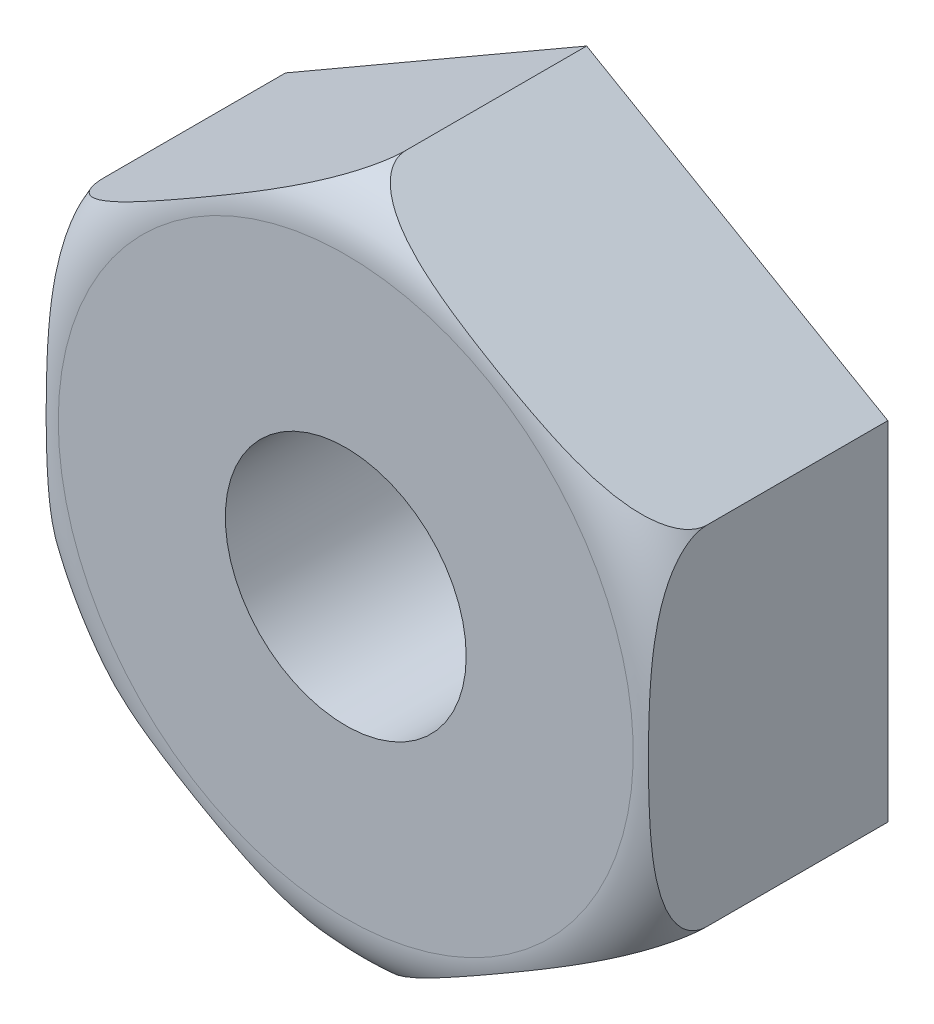
SolidWorks part; units mm, degrees
ref_plane "Front Plane" through (0, 0, 0) normal (0, 0, 1) x (1, 0, 0)
ref_plane "Top Plane" through (0, 0, 0) normal (0, 1, 0) x (1, 0, 0)
ref_plane "Right Plane" through (0, 0, 0) normal (1, 0, 0) x (0, 0, -1)
sketch "Sketch1" plane through (0, 0, 0) normal (0, 0, 1) x (1, 0, 0)
  line L1 (0, -5.7735) -> (5, -2.8868)
  line L2 (5, -2.8868) -> (5, 2.8868)
  line L3 (5, 2.8868) -> (0, 5.7735)
  line L4 (0, 5.7735) -> (-5, 2.8868)
  line L5 (-5, 2.8868) -> (-5, -2.8868)
  line L6 (-5, -2.8868) -> (0, -5.7735)
  circle A0 centre (0, 0) radius 5 construction
  dimension "D1" = 10
extrude "Boss-Extrude1" add sketch "Sketch1" along normal mid plane 4
sketch "Sketch3" plane through (0, 0, 0) normal (1, 0, 0) x (0, 0, -1)
  line L0 (-2, 4.7735) -> (-3.339, 5.4291)
  line L1 (-2, 2.8868) -> (-2, 5.7735) construction
  line L2 (-3.339, 5.4291) -> (-2.1424, 6.3329)
  line L3 (-2.1424, 6.3329) -> (-1, 5.7735)
  line L4 (-2, 5.7735) -> (2, 5.7735) construction
  line L5 (0, 0) -> (-5.1052, 0) construction
  arc A0 (-2, 4.7735) -> (-1, 5.7735) centre (-1, 4.7735) cw
  point P12 (-2, 5.7735)
  dimension "D1" = 1
revolve "Cut-Revolve2" cut sketch "Sketch3" angle 360 about L5
sketch "Sketch4" plane through (0, 0, 2) normal (0, 0, 1) x (1, 0, 0)
  circle A0 centre (0, 0) radius 2
  dimension "D1" = 2
extrude "Cut-Extrude1" cut sketch "Sketch4" against normal blind 10
